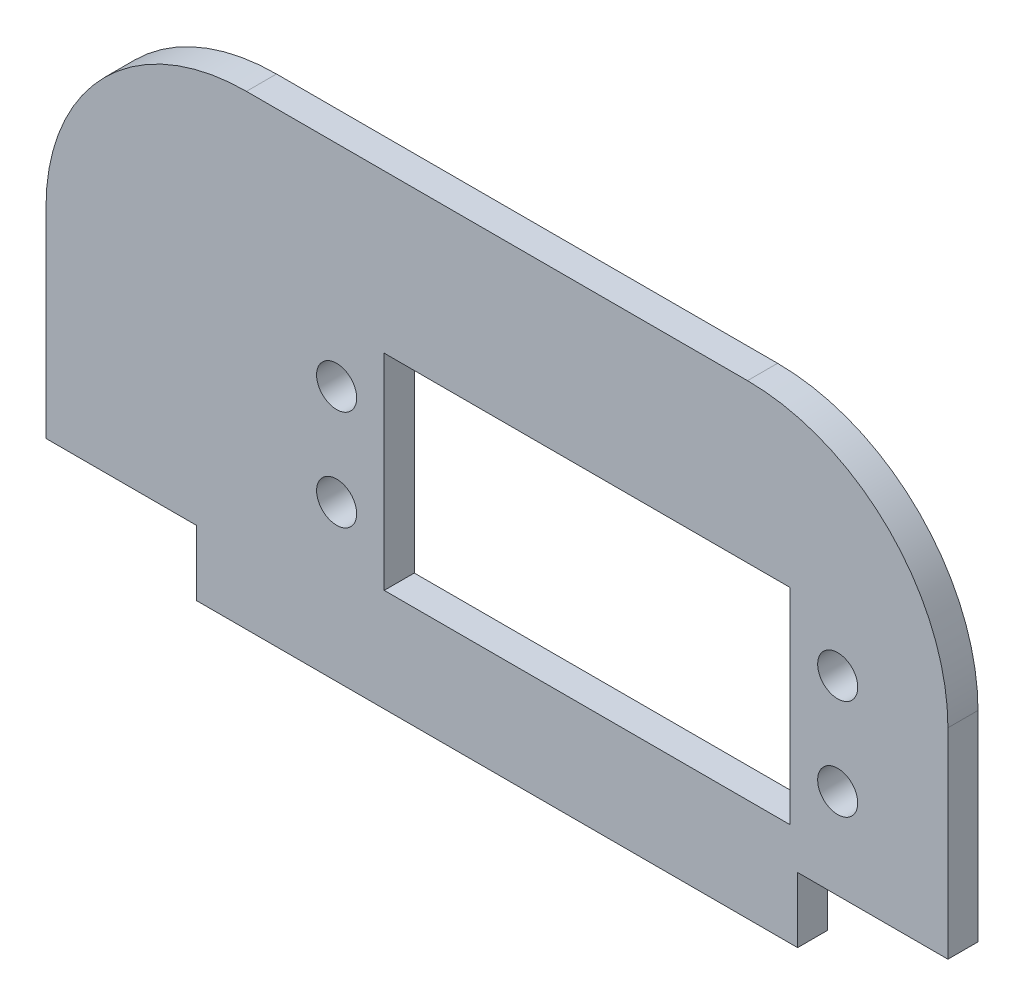
SolidWorks part; units mm, degrees
material "Balsa"
ref_plane "Alzado" through (0, 0, 0) normal (0, 0, 1) x (1, 0, 0)
ref_plane "Planta" through (0, 0, 0) normal (0, 1, 0) x (1, 0, 0)
ref_plane "Vista lateral" through (0, 0, 0) normal (1, 0, 0) x (0, 0, -1)
sketch "Croquis1" plane through (0, 0, 0) normal (0, 0, 1) x (1, 0, 0)
  line L1 (-45, -20) -> (-30, -20)
  line L2 (-45, -20) -> (-45, 20)
  line L3 (-45, 20) -> (45, 20)
  line L4 (45, -20) -> (45, 20)
  line L8 (-30, -20) -> (-30, -26.5)
  line L9 (-30, -26.5) -> (30, -26.5)
  line L10 (30, -20) -> (30, -26.5)
  line L15 (30, -20) -> (45, -20)
  point P0 (0, 0)
  point P6 (0, -10)
  point P7 (0, -10)
  dimension "D1" = 90
  dimension "D2" = 40
  dimension "D3" = 10
  dimension "D4" = 60
  dimension "D5" = 6.5
  dimension "D6" = 45
  dimension "D7" = 15
extrude "Saliente-Extruir1" add sketch "Croquis1" along normal blind 3
sketch "Croquis2" plane through (0, 0, 3) normal (0, 0, 1) x (1, 0, 0)
  line L1 (-11.25, 4.25) -> (29.25, 4.25)
  line L2 (-11.25, 4.25) -> (-11.25, -16.25)
  line L3 (-11.25, -16.25) -> (29.25, -16.25)
  line L4 (29.25, 4.25) -> (29.25, -16.25)
  line L5 (-11.25, 4.25) -> (29.25, -16.25) construction
  line L6 (-11.25, -16.25) -> (29.25, 4.25) construction
  point P0 (9, -6)
  point P1 (9, -6)
  dimension "D1" = 6
  dimension "D2" = 9
  dimension "D3" = 40.5
  dimension "D4" = 20.5
extrude "Cortar-Extruir1" cut sketch "Croquis2" against normal up to next
fillet "Redondeo1" radius 20 2 edges at (45, 20, 1.5) (-45, 20, 1.5)
sketch "Croquis3" plane through (0, 0, 3) normal (0, 0, 1) x (1, 0, 0)
  line L0 (9, -6) -> (9, -2.3191) construction
  line L1 (9, -2.3191) -> (9, -6) construction
  line L2 (9, -6) -> (11.3569, -6) construction
  circle A4 centre (34, -1) radius 2
  circle A5 centre (-16, -1) radius 2
  circle A6 centre (34, -11) radius 2
  circle A7 centre (-16, -11) radius 2
  point P0 (9, -6)
  dimension "D2" = 9
  dimension "D3" = 5
  dimension "D1" = 6
  dimension "D4" = 25
extrude "Cortar-Extruir2" cut sketch "Croquis3" against normal up to next
